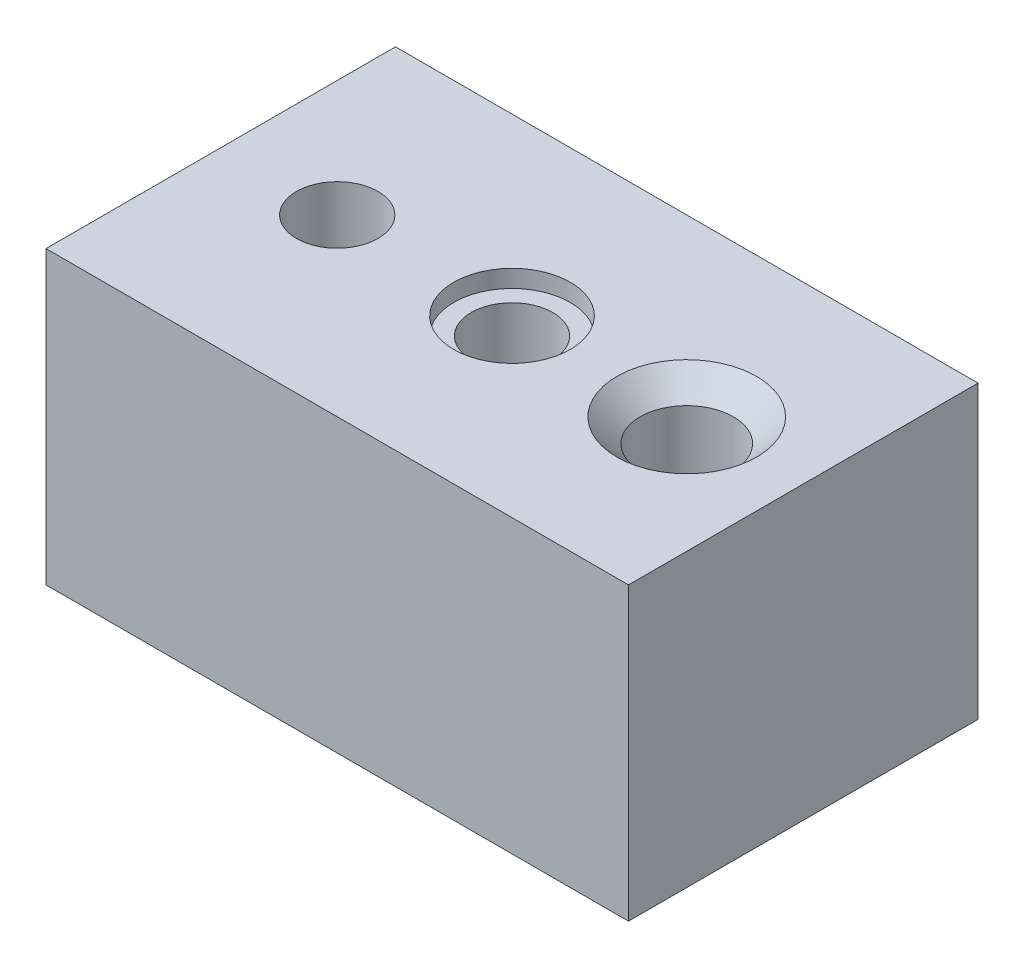
SolidWorks part; units mm, degrees
ref_plane "Front Plane" through (0, 0, 0) normal (0, 0, 1) x (1, 0, 0)
ref_plane "Top Plane" through (0, 0, 0) normal (0, 1, 0) x (1, 0, 0)
ref_plane "Right Plane" through (0, 0, 0) normal (1, 0, 0) x (0, 0, -1)
sketch "Sketch1" plane through (0, 0, 0) normal (0, 1, 0) x (1, 0, 0)
  line L1 (0, 0) -> (100, 0)
  line L2 (0, 0) -> (0, 60)
  line L3 (0, 60) -> (100, 60)
  line L4 (100, 0) -> (100, 60)
  dimension "D1" = 100
  dimension "D2" = 60
extrude "Boss-Extrude1" add sketch "Sketch1" against normal blind 50
hole_wizard "CBORE for M5 Hex Head Bolt1" positions "Sketch3" profile "Sketch4" counterbore size "M5" standard "ANSI Metric"
sketch "Sketch3" plane through (0, 0, 0) normal (0, 1, 0) x (1, 0, 0)
  line L0 (0, 60) -> (0, 0) construction
  line L1 (0, 0) -> (100, 0) construction
  point P0 (50, 30)
  dimension "D1" = 50
  dimension "D2" = 30
sketch "Sketch4" plane through (50, 0, -30) normal (1, 0, 0) x (0, 0, 1)
  line L0 (0, 0) -> (0, 20.206)
  line L1 (0, 20.206) -> (7, 16)
  line L2 (7, 16) -> (7, 3)
  line L3 (7, 3) -> (10, 3)
  line L4 (10, 3) -> (10, 0)
  line L5 (10, 0) -> (0, 0)
  line L10 (0, 20.206) -> (-7, 16) construction
  line L11 (0, -6.35) -> (0, 107.95) construction
  dimension "Hole Dia." = 14
  dimension "Hole Depth" = 16
  dimension "C'Bore Dia." = 20
  dimension "C'Bore Depth" = 3
  dimension "Drill Angle" = 118
hole_wizard "CSK for M5 Flat Head Machine Screw1" positions "Sketch5" profile "Sketch6" countersink size "M5" standard "ANSI Metric"
sketch "Sketch5" plane through (0, 0, 0) normal (0, 1, 0) x (1, 0, 0)
  line L0 (100, 60) -> (0, 60) construction
  point P0 (80, 30)
  dimension "D1" = 30
  dimension "D2" = 30
sketch "Sketch6" plane through (80, 0, -30) normal (1, 0, 0) x (0, 0, 1)
  line L0 (0, 0) -> (0, 20.8069)
  line L1 (0, 20.8069) -> (8, 16)
  line L2 (8, 16) -> (8, 4)
  line L3 (8, 4) -> (12, 0)
  line L5 (12, 0) -> (0, 0)
  line L6 (-8, 4) -> (-12, 0) construction
  line L10 (0, 20.8069) -> (-8, 16) construction
  line L11 (0, -6.35) -> (0, 107.95) construction
  dimension "Hole Dia." = 16
  dimension "Hole Depth" = 16
  dimension "Near C'Sink Dia." = 24
  dimension "Near C'Sink Angle" = 90
  dimension "Drill Angle" = 118
hole_wizard "M16x2.0 Tapped Hole1" positions "Sketch7" profile "Sketch8" tap size "M16x2.0" standard "ANSI Metric" end condition through all
sketch "Sketch7" plane through (0, 0, 0) normal (0, 1, 0) x (1, 0, 0)
  line L0 (100, 60) -> (0, 60) construction
  point P0 (20, 30)
  dimension "D1" = 30
  dimension "D2" = 30
sketch "Sketch8" plane through (20, 0, -30) normal (1, 0, 0) x (0, 0, 1)
  line L0 (0, 0) -> (0, 50)
  line L1 (0, 50) -> (7, 50)
  line L2 (7, 50) -> (7, 0)
  line L5 (7, 0) -> (0, 0)
  line L11 (0, -6.35) -> (0, 107.95) construction
  dimension "Thru Tap Drill Dia." = 14
  dimension "Thru Tap Drill Depth" = 50
cosmetic thread "Hole Thread1" parameters "D2"=16
